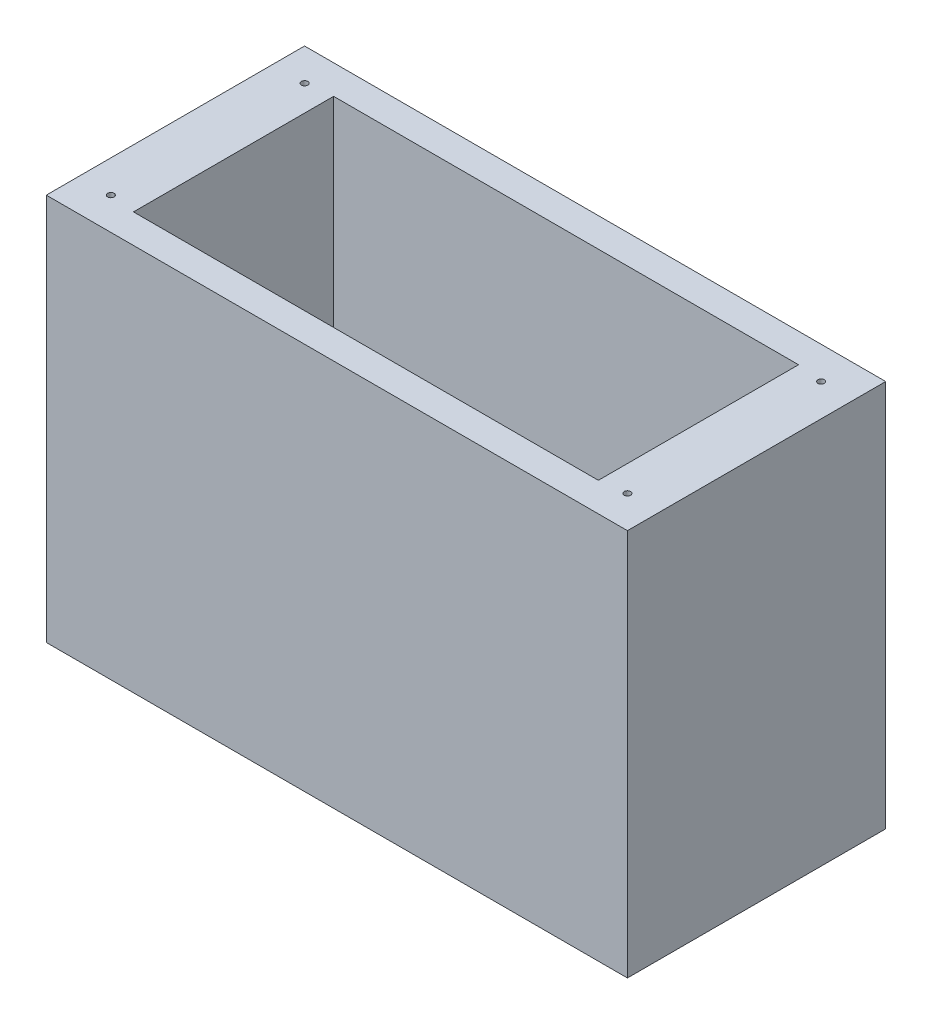
SolidWorks part; units mm, degrees
ref_plane "Front Plane" through (0, 0, 0) normal (0, 0, 1) x (1, 0, 0)
ref_plane "Top Plane" through (0, 0, 0) normal (0, 1, 0) x (1, 0, 0)
ref_plane "Right Plane" through (0, 0, 0) normal (1, 0, 0) x (0, 0, -1)
sketch "Sketch4" plane through (0, 0, 0) normal (0, 1, 0) x (1, 0, 0)
  line L1 (0, 0) -> (228.6, 0)
  line L2 (0, 0) -> (0, 101.6)
  line L3 (0, 101.6) -> (228.6, 101.6)
  line L4 (228.6, 0) -> (228.6, 101.6)
  dimension "D1" = 228.6
  dimension "D2" = 101.6
extrude "Boss-Extrude2" add sketch "Sketch4" along normal blind 152.4
sketch "Sketch5" plane through (0, 152.4, 0) normal (0, 1, 0) x (1, 0, 0)
  line L0 (0, 101.6) -> (0, 0) construction
  line L1 (22.86, 90.17) -> (205.74, 90.17)
  line L2 (22.86, 90.17) -> (22.86, 11.43)
  line L3 (22.86, 11.43) -> (205.74, 11.43)
  line L4 (205.74, 90.17) -> (205.74, 11.43)
  line L5 (228.6, 0) -> (228.6, 101.6) construction
  line L6 (228.6, 101.6) -> (0, 101.6) construction
  line L7 (0, 0) -> (228.6, 0) construction
  dimension "D1" = 22.86
  dimension "D2" = 22.86
  dimension "D3" = 11.43
  dimension "D4" = 11.43
extrude "Cut-Extrude3" cut sketch "Sketch5" against normal blind 139.7
sketch "Sketch6" plane through (0, 152.4, 0) normal (0, 1, 0) x (1, 0, 0)
  line L0 (114.3, 101.6) -> (114.3, 0) construction
  line L1 (228.6, 101.6) -> (0, 101.6) construction
  line L2 (0, 0) -> (228.6, 0) construction
  line L3 (0, 50.8) -> (228.6, 50.8) construction
  line L4 (0, 101.6) -> (0, 0) construction
  line L5 (228.6, 0) -> (228.6, 101.6) construction
  circle A0 centre (12.7, 88.9) radius 1.27
  circle A1 centre (215.9, 88.9) radius 1.27
  circle A2 centre (12.7, 12.7) radius 1.27
  circle A3 centre (215.9, 12.7) radius 1.27
  dimension "D1" = 2.54
  dimension "D3" = 12.7
  dimension "D2" = 12.7
extrude "Cut-Extrude4" cut sketch "Sketch6" against normal through all
